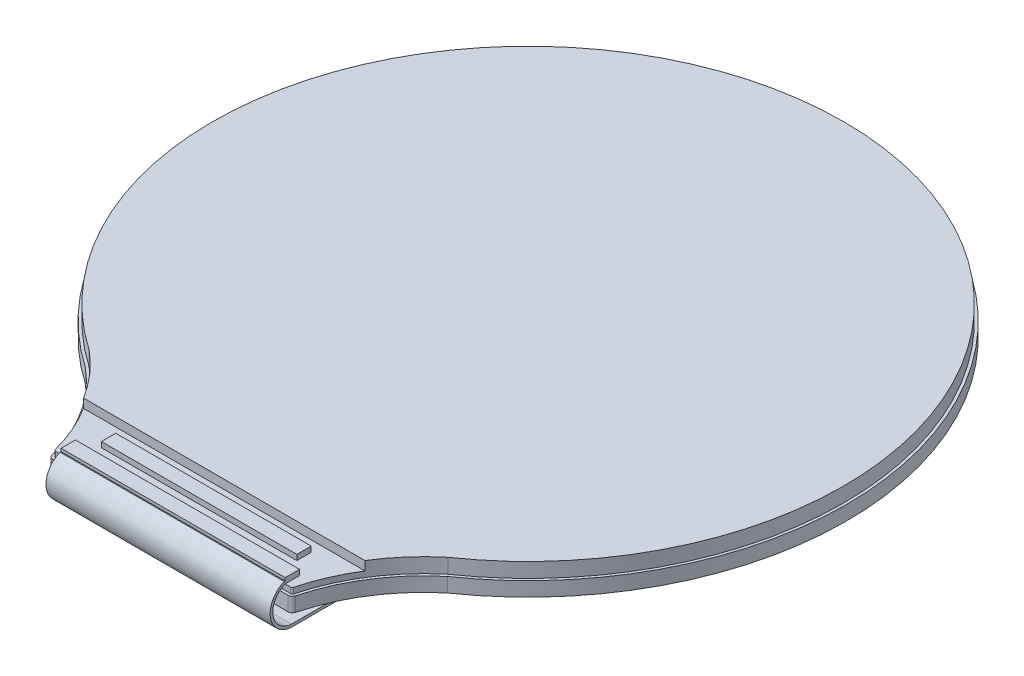
SolidWorks part; units mm, degrees
ref_plane "Front Plane" through (0, 0, 0) normal (0, 0, 1) x (1, 0, 0)
ref_plane "Top Plane" through (0, 0, 0) normal (0, 1, 0) x (1, 0, 0)
ref_plane "Right Plane" through (0, 0, 0) normal (1, 0, 0) x (0, 0, -1)
sketch "Sketch1" plane through (0, 0, 0) normal (0, 1, 0) x (1, 0, 0)
  line L0 (0, 17.75) -> (0, -19.95) construction
  line L1 (-6.75, -19.95) -> (6.75, -19.95)
  circle A0 centre (0, 0) radius 17.75
  arc A1 (-6.75, -19.95) -> (-10.0986, -14.5973) centre (-16.4685, -22.306) ccw
  arc A2 (6.75, -19.95) -> (10.0986, -14.5973) centre (16.4685, -22.306) cw
  point P8 (0, -19.95)
  dimension "D1" = 35.5
  dimension "D4" = 10
  dimension "D2" = 37.7
  dimension "D3" = 13.5
extrude "Boss-Extrude1" add sketch "Sketch1" along normal blind 0.8 contours A0 L0 L1 A2 | L0 A0 A1 L1 | L0 A0 | A0 L0
fillet "Fillet1" radius 0.25 2 edges at (6.75, 0.4, 19.95) (-6.75, 0.4, 19.95)
sketch "Sketch2" plane through (0, 0.8, 0) normal (0, 1, 0) x (1, 0, 0)
  line L1 (-6.5553, -19.8) -> (6.5553, -19.8)
  line L3 (-6.5553, -19.95) -> (6.5553, -19.95)
  line L4 (-6.5553, -19.95) -> (6.5553, -19.95) construction
  arc A3 (6.5553, -19.8) -> (6.652, -19.7254) centre (6.5553, -19.7) ccw
  arc A4 (10.0081, -14.4775) -> (6.652, -19.7254) centre (16.4685, -22.306) ccw
  arc A5 (10.0081, -14.4775) -> (-10.0081, -14.4775) centre (0, 0) ccw
  arc A9 (-6.652, -19.7254) -> (-10.0081, -14.4775) centre (-16.4685, -22.306) ccw
  arc A10 (-6.652, -19.7254) -> (-6.5553, -19.8) centre (-6.5553, -19.7) ccw
  arc A11 (6.5553, -19.95) -> (6.7971, -19.7636) centre (6.5553, -19.7) ccw
  arc A12 (10.0986, -14.5973) -> (6.7971, -19.7636) centre (16.4685, -22.306) ccw
  arc A13 (10.0986, -14.5973) -> (-10.0986, -14.5973) centre (0, 0) ccw
  arc A14 (-6.7971, -19.7636) -> (-10.0986, -14.5973) centre (-16.4685, -22.306) ccw
  arc A15 (-6.7971, -19.7636) -> (-6.5553, -19.95) centre (-6.5553, -19.7) ccw
  arc A16 (6.5553, -19.95) -> (6.7971, -19.7636) centre (6.5553, -19.7) ccw construction
  arc A17 (10.0986, -14.5973) -> (6.7971, -19.7636) centre (16.4685, -22.306) ccw construction
  arc A18 (10.0986, -14.5973) -> (-10.0986, -14.5973) centre (0, 0) ccw construction
  arc A19 (-6.7971, -19.7636) -> (-10.0986, -14.5973) centre (-16.4685, -22.306) ccw construction
  arc A20 (-6.7971, -19.7636) -> (-6.5553, -19.95) centre (-6.5553, -19.7) ccw construction
  dimension "D1" = 0
  dimension "D2" = 0.15
extrude "Boss-Extrude2" add sketch "Sketch2" along normal blind 0.82
sketch "Sketch4" plane through (0, 1.62, 0) normal (0, 1, 0) x (1, 0, 0)
  line L0 (0, 0) -> (0, -19.95) construction
  line L1 (-6.5553, -19.95) -> (6.5553, -19.95) construction
  line L2 (10, -16.95) -> (-10, -16.95)
  line L5 (-10, -16.95) -> (-10, -19.95)
  line L6 (-10, -19.95) -> (10, -19.95)
  line L7 (10, -16.95) -> (10, -19.95)
  point P8 (0, -16.95)
  dimension "D1" = 3
  dimension "D2" = 20
  dimension "D3" = 3
extrude "Cut-Extrude1" cut sketch "Sketch4" against normal blind 0.5
sketch "Sketch5" plane through (0, 1.12, 0) normal (0, 1, 0) x (1, 0, 0)
  line L0 (0, -19.95) -> (0, -16.95) construction
  line L1 (-6.5553, -19.95) -> (6.5553, -19.95) construction
  line L2 (7.8467, -16.95) -> (-7.8467, -16.95) construction
  line L3 (7.8467, -16.95) -> (-7.8467, -16.95) construction
  line L4 (-5.45, -17.55) -> (5.45, -17.55)
  line L5 (-5.45, -17.55) -> (-5.45, -18.35)
  line L6 (-5.45, -18.35) -> (5.45, -18.35)
  line L7 (5.45, -17.55) -> (5.45, -18.35)
  line L8 (-5.45, -17.55) -> (5.45, -18.35) construction
  line L9 (-5.45, -18.35) -> (5.45, -17.55) construction
  line L10 (-6.25, -19) -> (6.25, -19)
  line L11 (-6.25, -19) -> (-6.25, -19.8)
  line L12 (-6.25, -19.8) -> (6.25, -19.8)
  line L13 (6.25, -19) -> (6.25, -19.8)
  line L14 (-6.25, -19) -> (6.25, -19.8) construction
  line L15 (-6.25, -19.8) -> (6.25, -19) construction
  line L16 (-6.5553, -19.8) -> (6.5553, -19.8) construction
  point P6 (0, -17.95)
  point P11 (0, -19.4)
  dimension "D1" = 0.8
  dimension "D2" = 0.8
  dimension "D3" = 0.6
  dimension "D4" = 12.5
  dimension "D5" = 10.9
extrude "Boss-Extrude3" add sketch "Sketch5" along normal blind 0.3
sketch "Sketch6" plane through (0, 0, 0) normal (0, -1, 0) x (1, 0, 0)
  line L0 (-17.2934, -4) -> (17.2934, -4) construction
  arc A0 (-10.0986, 14.5973) -> (10.0986, 14.5973) centre (0, 0) ccw construction
  text T0 "LCD GC9A01" font "Arial" height 2
  dimension "D1" = 4
extrude "Cut-Extrude2" cut sketch "Sketch6" against normal blind 0.001
sketch "Sketch8" plane through (0, 0, 0) normal (1, 0, 0) x (0, 0, -1)
  line L0 (-19.45, -1) -> (-10.65, -1)
  line L1 (-19.7636, 0) -> (-14.5973, 0) construction
  line L2 (-19.95, 0) -> (-19.95, 0.8) construction
  line L3 (-19.4538, -1.15) -> (-10.65, -1.15)
  line L4 (-19.8556, 1.2593) -> (-19.8, 1.2593)
  line L6 (-19.8, 1.42) -> (-19.8, 1.12) construction
  line L7 (-19.8, 1.2593) -> (-19.8, 1.12)
  line L8 (-10.65, -1) -> (-10.65, -1.15)
  arc A0 (-19.8, 1.12) -> (-19.45, -1) centre (-19.392, 0.0985) ccw
  arc A1 (-19.8556, 1.2593) -> (-19.4538, -1.15) centre (-19.392, 0.0985) ccw
  dimension "D3" = 1.1
  dimension "D1" = 1
  dimension "D2" = 9.3
  dimension "D4" = 0.5
  dimension "D5" = 0.15
extrude "Boss-Extrude4" add sketch "Sketch8" along normal mid plane 12.5 separate body
sketch "Sketch9" plane through (0, -1.15, 0) normal (0, -1, 0) x (1, 0, 0)
  line L0 (-5.15, 19.95) -> (-5.15, 14.45) construction
  line L1 (-6.5553, 19.95) -> (6.5553, 19.95) construction
  line L2 (-6.25, 19.4538) -> (-6.25, 10.65) construction
  line L3 (0, 19.95) -> (0, 10.65) construction
  line L4 (6.25, 10.65) -> (-6.25, 10.65) construction
  circle A0 centre (-5.15, 14.45) radius 0.5
  circle A1 centre (5.15, 14.45) radius 0.5
  dimension "D3" = 1
  dimension "D1" = 5.5
  dimension "D2" = 1.1
extrude "Cut-Extrude3" cut sketch "Sketch9" against normal blind 0.2
sketch "Sketch10" plane through (0, -1.15, 0) normal (0, -1, 0) x (1, 0, 0)
  line L0 (-6.25, 19.4538) -> (-6.25, 10.65) construction
  line L1 (6.25, 10.65) -> (5.15, 10.65)
  line L2 (6.25, 10.65) -> (6.25, 14.15)
  line L3 (6.25, 14.15) -> (6.15, 14.15)
  line L4 (5.15, 10.65) -> (5.15, 13.15)
  arc A0 (6.15, 14.15) -> (5.15, 13.15) centre (6.15, 13.15) ccw
  dimension "D3" = 1
  dimension "D1" = 11.4
  dimension "D2" = 3.5
extrude "Cut-Extrude4" cut sketch "Sketch10" against normal blind 0.2
fillet "Fillet2" radius 0.5 1 edges at (6.25, -1.075, 14.15)
fillet "Fillet3" radius 0.5 2 edges at (5.15, -1.075, 10.65) (-6.25, -1.075, 10.65)
sketch "Sketch11" plane through (0, -1.15, 0) normal (0, -1, 0) x (1, 0, 0)
  line L0 (4.65, 10.65) -> (-5.75, 10.65) construction
  line L1 (-4.65, 10.65) -> (-4.15, 10.65)
  line L2 (-4.65, 10.65) -> (-4.65, 12.65)
  line L3 (-4.65, 12.65) -> (-4.15, 12.65)
  line L4 (-4.15, 10.65) -> (-4.15, 12.65)
  line L5 (-6.25, 19.4538) -> (-6.25, 11.15) construction
  line L6 (-3.95, 10.65) -> (-3.45, 10.65)
  line L7 (-3.95, 10.65) -> (-3.95, 12.65)
  line L8 (-3.95, 12.65) -> (-3.45, 12.65)
  line L9 (-3.45, 10.65) -> (-3.45, 12.65)
  line L10 (-3.25, 10.65) -> (-2.75, 10.65)
  line L11 (-3.25, 10.65) -> (-3.25, 12.65)
  line L12 (-3.25, 12.65) -> (-2.75, 12.65)
  line L13 (-2.75, 10.65) -> (-2.75, 12.65)
  line L14 (-2.55, 10.65) -> (-2.05, 10.65)
  line L15 (-2.55, 10.65) -> (-2.55, 12.65)
  line L16 (-2.55, 12.65) -> (-2.05, 12.65)
  line L17 (-2.05, 10.65) -> (-2.05, 12.65)
  line L18 (-1.85, 10.65) -> (-1.35, 10.65)
  line L19 (-1.85, 10.65) -> (-1.85, 12.65)
  line L20 (-1.85, 12.65) -> (-1.35, 12.65)
  line L21 (-1.35, 10.65) -> (-1.35, 12.65)
  line L22 (-1.15, 10.65) -> (-0.65, 10.65)
  line L23 (-1.15, 10.65) -> (-1.15, 12.65)
  line L24 (-1.15, 12.65) -> (-0.65, 12.65)
  line L25 (-0.65, 10.65) -> (-0.65, 12.65)
  line L26 (-0.45, 10.65) -> (0.05, 10.65)
  line L27 (-0.45, 10.65) -> (-0.45, 12.65)
  line L28 (-0.45, 12.65) -> (0.05, 12.65)
  line L29 (0.05, 10.65) -> (0.05, 12.65)
  line L30 (0.25, 10.65) -> (0.75, 10.65)
  line L31 (0.25, 10.65) -> (0.25, 12.65)
  line L32 (0.25, 12.65) -> (0.75, 12.65)
  line L33 (0.75, 10.65) -> (0.75, 12.65)
  line L34 (0.95, 10.65) -> (1.45, 10.65)
  line L35 (0.95, 10.65) -> (0.95, 12.65)
  line L36 (0.95, 12.65) -> (1.45, 12.65)
  line L37 (1.45, 10.65) -> (1.45, 12.65)
  line L38 (1.65, 10.65) -> (2.15, 10.65)
  line L39 (1.65, 10.65) -> (1.65, 12.65)
  line L40 (1.65, 12.65) -> (2.15, 12.65)
  line L41 (2.15, 10.65) -> (2.15, 12.65)
  line L42 (2.35, 10.65) -> (2.85, 10.65)
  line L43 (2.35, 10.65) -> (2.35, 12.65)
  line L44 (2.35, 12.65) -> (2.85, 12.65)
  line L45 (2.85, 10.65) -> (2.85, 12.65)
  line L46 (3.05, 10.65) -> (3.55, 10.65)
  line L47 (3.05, 10.65) -> (3.05, 12.65)
  line L48 (3.05, 12.65) -> (3.55, 12.65)
  line L49 (3.55, 10.65) -> (3.55, 12.65)
  line L50 (5.15, 13.15) -> (5.15, 11.15) construction
  dimension "D1" = 0.5
  dimension "D2" = 2
  dimension "D3" = 1.6
  dimension "D5" = 1.6
  dimension "D4" = 12
extrude "Cut-Extrude5" cut sketch "Sketch11" against normal blind 0.01
